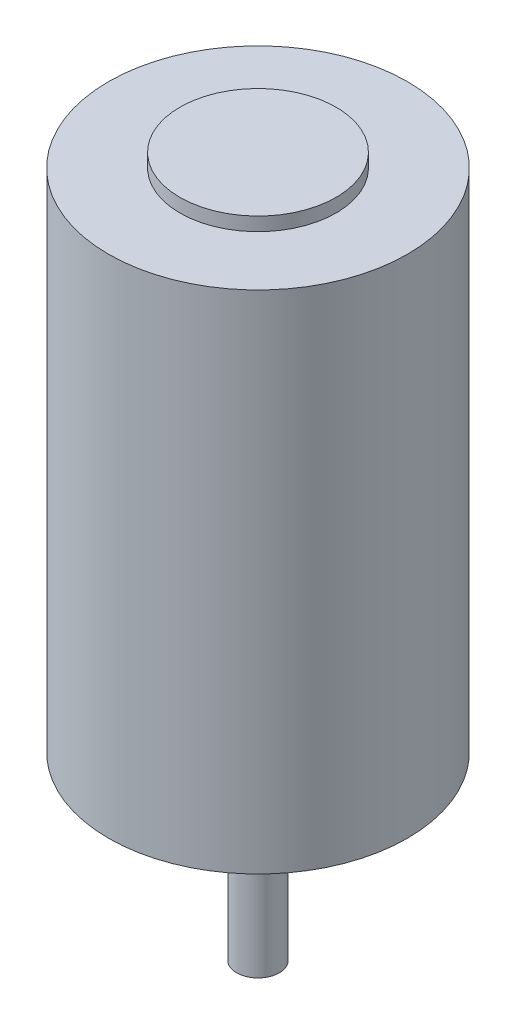
SolidWorks part; units mm, degrees
ref_plane "Front Plane" through (0, 0, 0) normal (0, 0, 1) x (1, 0, 0)
ref_plane "Top Plane" through (0, 0, 0) normal (0, 1, 0) x (1, 0, 0)
ref_plane "Right Plane" through (0, 0, 0) normal (1, 0, 0) x (0, 0, -1)
sketch "Sketch2" plane through (0, 0, 0) normal (0, 1, 0) x (1, 0, 0)
  circle A0 centre (0, 0) radius 21.0185
  dimension "D1" = 42.037
extrude "Boss-Extrude1" add sketch "Sketch2" along normal blind 71.12
sketch "Sketch3" plane through (0, 71.12, 0) normal (0, 1, 0) x (1, 0, 0)
  circle A0 centre (0, 0) radius 10.9855
  dimension "D1" = 21.971
extrude "Boss-Extrude2" add sketch "Sketch3" along normal blind 1.905
sketch "Sketch4" plane through (0, 0, 0) normal (0, -1, 0) x (1, 0, 0)
  circle A0 centre (0, 0) radius 10.9855
  circle A1 centre (0, 0) radius 8.4455
  dimension "D1" = 21.971
  dimension "D2" = 16.891
extrude "Boss-Extrude3" add sketch "Sketch4" along normal blind 1.905
sketch "Sketch5" plane through (0, 0, 0) normal (0, -1, 0) x (1, 0, 0)
  circle A0 centre (0, 0) radius 3
  dimension "D1" = 6
extrude "Boss-Extrude4" add sketch "Sketch5" along normal blind 25.4
sketch "Sketch6" plane through (0, 0, 0) normal (0, -1, 0) x (1, 0, 0)
  circle A0 centre (0, 0) radius 5.08
  dimension "D1" = 10.16
extrude "Boss-Extrude5" add sketch "Sketch6" along normal blind 3.429
sketch "Sketch7" plane through (0, 0, 0) normal (0, -1, 0) x (1, 0, 0)
  line L0 (0, 0) -> (0, 19.9779) construction
  circle A0 centre (15.875, 0) radius 1.27
  circle A1 centre (-15.875, 0) radius 1.27
  dimension "D1" = 2.54
  dimension "D2" = 15.875
extrude "Cut-Extrude1" cut sketch "Sketch7" against normal blind 5.08
